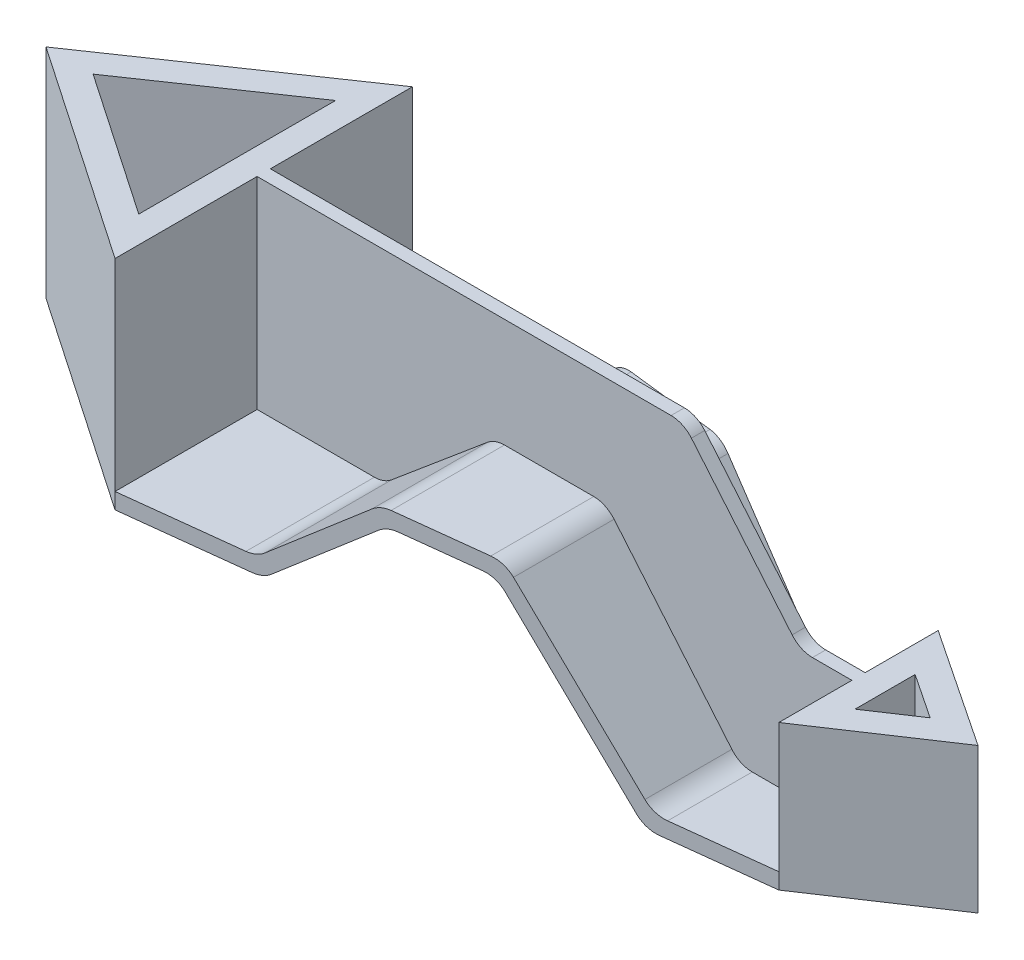
SolidWorks part; units mm, degrees
material "1060 Alloy"
ref_plane "Front Plane" through (0, 0, 0) normal (0, 0, 1) x (1, 0, 0)
ref_plane "Top Plane" through (0, 0, 0) normal (0, 1, 0) x (1, 0, 0)
ref_plane "Right Plane" through (0, 0, 0) normal (1, 0, 0) x (0, 0, -1)
sketch "Sketch2" plane through (0, 0, 0) normal (0, 1, 0) x (1, 0, 0)
  line L0 (0, -56) -> (0, 56)
  line L1 (0, 56) -> (-82, 0)
  line L2 (-82, 0) -> (0, -56)
  line L3 (-10, 37.0613) -> (-64.2683, 0)
  line L4 (-64.2683, 0) -> (-10, -37.0613)
  line L5 (-10, -37.0613) -> (-10, 37.0613)
  point P4 (0, 0)
  dimension "D1" = 56
  dimension "D2" = 82
  dimension "D3" = 10
extrude "Boss-Extrude1" add sketch "Sketch2" along normal blind 82
sketch "Sketch3" plane through (0, 0, 0) normal (0, 0, 1) x (1, 0, 0)
  line L0 (0, 0) -> (50, 0)
  line L1 (50, 0) -> (91.7114, 35)
  line L2 (91.7114, 35) -> (128.654, 35)
  line L3 (128.654, 35) -> (179, -25)
  line L4 (179, -25) -> (224, -25)
  line L5 (0, 6) -> (47.8162, 6)
  line L6 (47.8162, 6) -> (89.5276, 41)
  line L7 (89.5276, 41) -> (131.4519, 41)
  line L8 (131.4519, 41) -> (181.7978, -19)
  line L9 (181.7978, -19) -> (224, -19)
  line L10 (0, 6) -> (0, 0)
  line L11 (224, -19) -> (224, -25)
  dimension "D1" = 50
  dimension "D2" = 35
  dimension "D3" = 60
  dimension "D4" = 45
  dimension "D5" = 140
  dimension "D6" = 130
  dimension "D7" = 224
  dimension "D8" = 6
extrude "Boss-Extrude2" add sketch "Sketch3" along normal mid plane 112
sketch "Sketch4" plane through (0, 0, 0) normal (0, 1, 0) x (1, 0, 0)
  line L0 (224, -30) -> (224, 30)
  line L1 (224, -56) -> (224, 56) construction
  line L2 (224, 30) -> (269, 0)
  line L3 (269, 0) -> (224, -30)
  line L4 (234, 11.3148) -> (250.9722, 0)
  line L5 (250.9722, 0) -> (234, -11.3148)
  line L6 (234, -11.3148) -> (234, 11.3148)
  point P5 (224, 0)
  dimension "D1" = 30
  dimension "D2" = 45
  dimension "D3" = 10
extrude "Boss-Extrude3" add sketch "Sketch4" along normal blind 54.6667 from surface at -25 starting at face at (201.5, -25, 0)
sketch "Sketch7" plane through (0, 0, 0) normal (0, 0, 1) x (1, 0, 0)
  line L0 (0, 82) -> (160.5786, 82)
  line L1 (160.5786, 82) -> (204.4915, 29.6667)
  line L2 (204.4915, 29.6667) -> (224, 29.6667)
  line L3 (128.654, 35) -> (179, -25) construction
  line L4 (0, 82) -> (0, 6)
  line L5 (0, 6) -> (47.8162, 6)
  line L6 (47.8162, 6) -> (89.5276, 41)
  line L7 (89.5276, 41) -> (131.4519, 41)
  line L8 (131.4519, 41) -> (181.7978, -19)
  line L9 (181.7978, -19) -> (224, -19)
  line L10 (224, -19) -> (224, 29.6667)
  dimension "D1" = 54.6667
extrude "Boss-Extrude4" add sketch "Sketch7" along normal mid plane 5
sketch "Sketch8" plane through (0, 0, 0) normal (0, 1, 0) x (1, 0, 0)
  line L0 (0, 56) -> (224, 56)
  line L1 (224, 56) -> (224, 30)
  line L2 (224, 30) -> (0, 56)
  line L3 (0, -56) -> (224, -30)
  line L4 (224, -30) -> (224, -56)
  line L5 (224, -56) -> (0, -56)
extrude "Cut-Extrude2" cut sketch "Sketch8" against normal through all both and the other way through all
fillet "Fillet1" radius 10 14 edges at (50, 0, 0) (91.7114, 35, 0) (179, -25, 0) (128.654, 35, 0) (204.4915, 29.6667, 0) (47.8162, 6, -26.475) (181.7978, -19, -18.6992) (89.5276, 41, -24.0542) (131.4519, 41, -21.6211) (181.7978, -19, 18.6992) (131.4519, 41, 21.6211) (47.8162, 6, 26.475) (89.5276, 41, 24.0542) (160.5786, 82, 0)
equation "\"A\"= 224"
equation "\"B\"= 82"
equation "\"D1@Sketch2\"=\"A\"/4"
equation "\"D2@Sketch2\"=\"B\""
equation "\"D1@Boss-Extrude1\"=\"B\""
equation "\"D7@Sketch3\"=\"A\""
equation "\"D1@Boss-Extrude2\"=\"A\"/2"
equation "\"D1@Boss-Extrude3\"=\"B\"*2/3"
equation "\"D1@Sketch7\"=\"B\"*2/3"
equation "\"D1@Boss-Extrude4\"=\"A\"/2"
